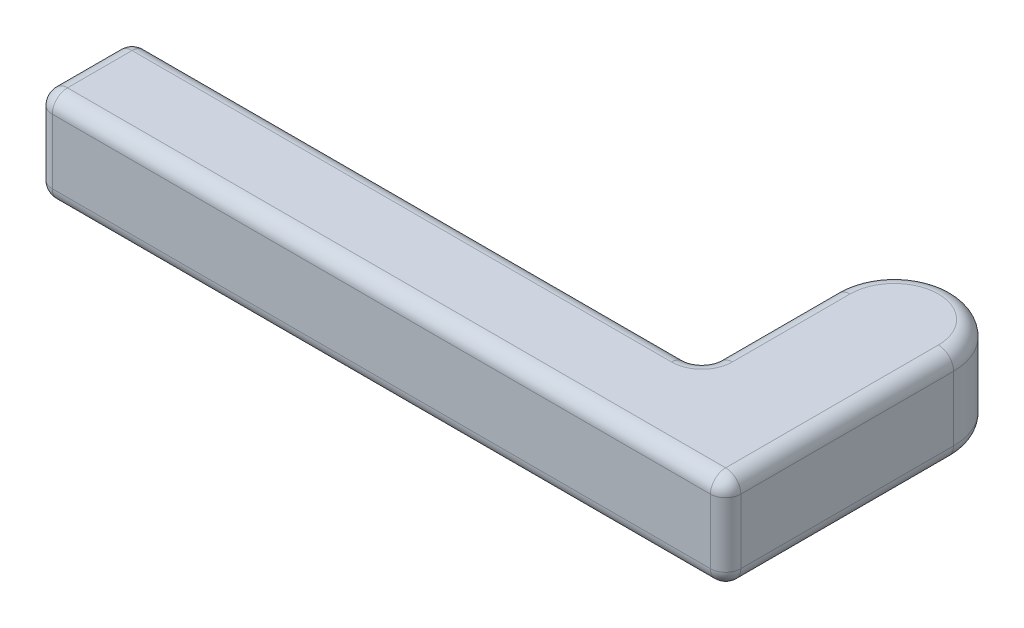
SolidWorks part; units mm, degrees
ref_plane "Front Plane" through (0, 0, 0) normal (0, 0, 1) x (1, 0, 0)
ref_plane "Top Plane" through (0, 0, 0) normal (0, 1, 0) x (1, 0, 0)
ref_plane "Right Plane" through (0, 0, 0) normal (1, 0, 0) x (0, 0, -1)
sketch "Sketch1" plane through (0, 0, 0) normal (0, 1, 0) x (1, 0, 0)
  line L0 (-13.3674, 0) -> (78.7076, 0)
  line L4 (62.8326, 12.7) -> (-13.3674, 12.7)
  line L5 (-13.3674, 12.7) -> (-13.3674, 0)
  line L7 (62.8326, 12.7) -> (62.8326, 30.48)
  line L9 (78.7076, 30.48) -> (78.7076, 0)
  arc A0 (78.7076, 30.48) -> (62.8326, 30.48) centre (70.7701, 30.48) ccw
  dimension "D1" = 92.075
  dimension "D2" = 76.2
  dimension "D3" = 12.7
  dimension "D4" = 17.78
extrude "Boss-Extrude2" add sketch "Sketch1" along normal blind 12.7
fillet "Fillet1" radius 2.032 16 edges at (-13.3674, 6.35, -12.7) (62.8326, 6.35, -12.7) (78.7076, 6.35, 0) (32.6701, 0, 0) (78.7076, 0, -15.24) (70.7701, 0, -38.4175) (62.8326, 0, -21.59) (24.7326, 0, -12.7) (-13.3674, 0, -6.35) (24.7326, 12.7, -12.7) (62.8326, 12.7, -21.59) (70.7701, 12.7, -38.4175) (78.7076, 12.7, -15.24) (32.6701, 12.7, 0) (-13.3674, 12.7, -6.35) (-13.3674, 6.35, 0)
